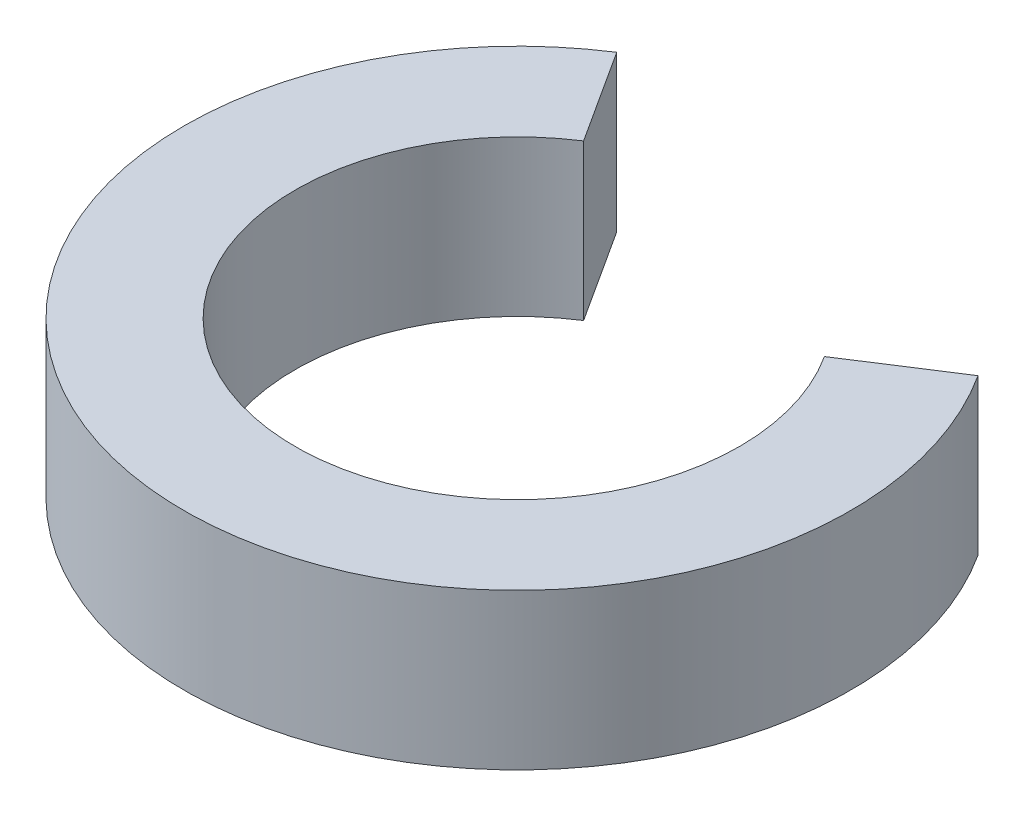
SolidWorks part; units mm, degrees
ref_plane "Спереди" through (0, 0, 0) normal (0, 0, 1) x (1, 0, 0)
ref_plane "Сверху" through (0, 0, 0) normal (0, 1, 0) x (1, 0, 0)
ref_plane "Справа" through (0, 0, 0) normal (1, 0, 0) x (0, 0, -1)
other "Configuration Table"
sketch "Эскиз1" plane through (0, 0, 0) normal (0, 1, 0) x (1, 0, 0)
  line L0 (-5.4199, 8.4039) -> (-8.1298, 12.6058)
  line L1 (8.4039, 5.4199) -> (12.6058, 8.1298)
  arc A0 (8.4039, 5.4199) -> (-5.4199, 8.4039) centre (0, 0) cw
  arc A2 (-8.1298, 12.6058) -> (12.6058, 8.1298) centre (0, 0) ccw
  dimension "D1" = 10
  dimension "D2" = 15
extrude "Бобышка-Вытянуть1" add sketch "Эскиз1" along normal blind 7
